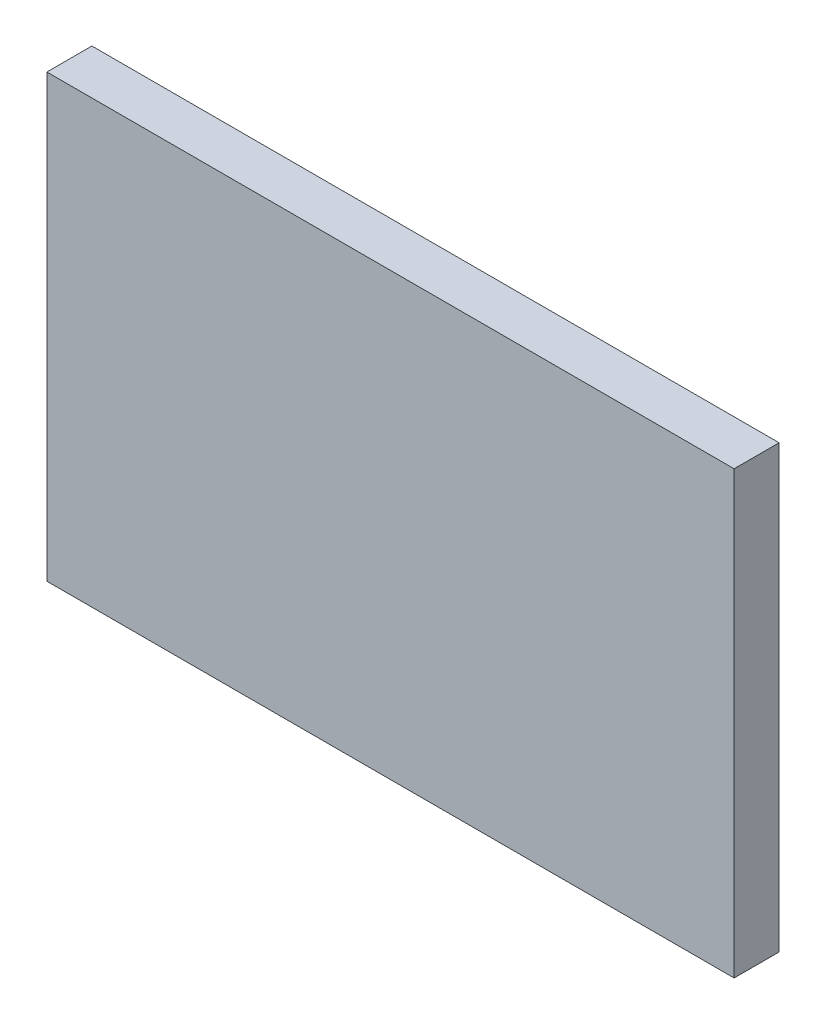
SolidWorks part; units mm, degrees
material "Glass"
ref_plane "Front Plane" through (0, 0, 0) normal (0, 0, 1) x (1, 0, 0)
ref_plane "Top Plane" through (0, 0, 0) normal (0, 1, 0) x (1, 0, 0)
ref_plane "Right Plane" through (0, 0, 0) normal (1, 0, 0) x (0, 0, -1)
sketch "Sketch1" plane through (0, 0, 0) normal (0, 0, 1) x (1, 0, 0)
  line L1 (-94.996, -60.96) -> (94.996, -60.96)
  line L2 (-94.996, -60.96) -> (-94.996, 60.96)
  line L3 (-94.996, 60.96) -> (94.996, 60.96)
  line L4 (94.996, -60.96) -> (94.996, 60.96)
  line L5 (-94.996, -60.96) -> (94.996, 60.96) construction
  line L6 (-94.996, 60.96) -> (94.996, -60.96) construction
  point P0 (0, 0)
  dimension "D1" = 121.92
  dimension "D2" = 189.992
extrude "Boss-Extrude1" add sketch "Sketch1" along normal blind 12.446
